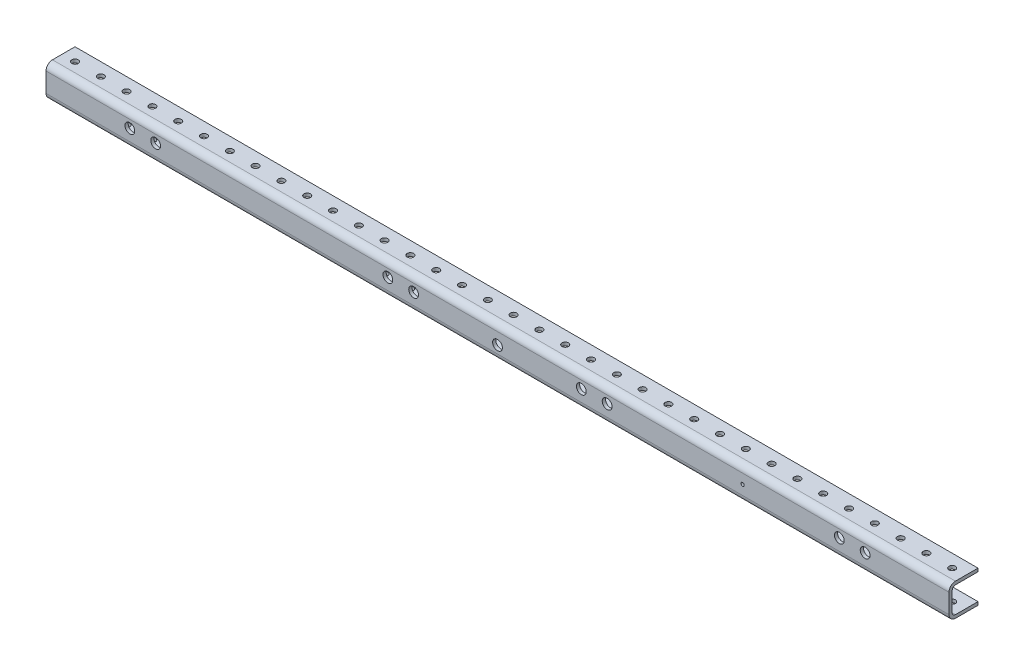
SolidWorks part; units mm, degrees
material "6061-T6 (SS)"
ref_plane "Front Plane" through (0, 0, 0) normal (0, 0, 1) x (1, 0, 0)
ref_plane "Top Plane" through (0, 0, 0) normal (0, 1, 0) x (1, 0, 0)
ref_plane "Right Plane" through (0, 0, 0) normal (1, 0, 0) x (0, 0, -1)
ref_plane "Plane1" through (0, 0, 3.175) normal (0, 0, 1) x (1, 0, 0)
sketch "Sketch1" plane through (0, 0, 3.175) normal (0, 0, 1) x (1, 0, 0)
  line L0 (872.98, -7.202) -> (872.98, 24.548)
  line L1 (872.98, 24.548) -> (-16.02, 24.548)
  line L2 (-16.02, 24.548) -> (-16.02, -7.202)
  line L3 (-16.02, -7.202) -> (872.98, -7.202)
extrude "Extrude1" add sketch "Sketch1" against normal blind 28.575
sketch "Sketch2" plane through (-16.02, 0, 0) normal (-1, 0, 0) x (0, 0, 1)
  line L0 (-25.4, 21.373) -> (-25.4, -4.027)
  line L1 (-25.4, -4.027) -> (0, -4.027)
  line L2 (0, -4.027) -> (0, 21.373)
  line L3 (0, 21.373) -> (-25.4, 21.373)
extrude "Extrude2" cut sketch "Sketch2" against normal through all
hole_wizard "Hole1" positions "Sketch4" profile "Sketch3" legacy
sketch "Sketch4" plane through (0, -4.027, 0) normal (0, 1, 0) x (-1, 0, 0)
  point P0 (3.32, -12.7)
sketch "Sketch3" plane through (-3.32, -4.027, -12.7) normal (1, 0, 0) x (0, 0, 1)
  line L0 (0, 0) -> (0, 3.175)
  line L1 (0, 3.175) -> (3.175, 3.175)
  line L2 (3.175, 3.175) -> (3.175, 0)
  line L3 (3.175, 0) -> (0, 0)
  line L4 (0, 110) -> (0, -10) construction
  dimension "Diameter" = 6.35
  dimension "Depth" = 3.175
hole_wizard "Hole2" positions "Sketch6" profile "Sketch5" legacy
sketch "Sketch6" plane through (0, -4.027, 0) normal (0, 1, 0) x (-1, 0, 0)
  point P0 (-22.08, -12.7)
sketch "Sketch5" plane through (22.08, -4.027, -12.7) normal (1, 0, 0) x (0, 0, 1)
  line L0 (0, 0) -> (0, 3.175)
  line L1 (0, 3.175) -> (3.175, 3.175)
  line L2 (3.175, 3.175) -> (3.175, 0)
  line L3 (3.175, 0) -> (0, 0)
  line L4 (0, 110) -> (0, -10) construction
  dimension "Diameter" = 6.35
  dimension "Depth" = 3.175
hole_wizard "Hole3" positions "Sketch8" profile "Sketch7" legacy
sketch "Sketch8" plane through (0, -4.027, 0) normal (0, 1, 0) x (-1, 0, 0)
  point P0 (-47.48, -12.7)
sketch "Sketch7" plane through (47.48, -4.027, -12.7) normal (1, 0, 0) x (0, 0, 1)
  line L0 (0, 0) -> (0, 3.175)
  line L1 (0, 3.175) -> (3.175, 3.175)
  line L2 (3.175, 3.175) -> (3.175, 0)
  line L3 (3.175, 0) -> (0, 0)
  line L4 (0, 110) -> (0, -10) construction
  dimension "Diameter" = 6.35
  dimension "Depth" = 3.175
hole_wizard "Hole4" positions "Sketch10" profile "Sketch9" legacy
sketch "Sketch10" plane through (0, -4.027, 0) normal (0, 1, 0) x (-1, 0, 0)
  point P0 (-72.88, -12.7)
sketch "Sketch9" plane through (72.88, -4.027, -12.7) normal (1, 0, 0) x (0, 0, 1)
  line L0 (0, 0) -> (0, 3.175)
  line L1 (0, 3.175) -> (3.175, 3.175)
  line L2 (3.175, 3.175) -> (3.175, 0)
  line L3 (3.175, 0) -> (0, 0)
  line L4 (0, 110) -> (0, -10) construction
  dimension "Diameter" = 6.35
  dimension "Depth" = 3.175
hole_wizard "Hole5" positions "Sketch12" profile "Sketch11" legacy
sketch "Sketch12" plane through (0, -4.027, 0) normal (0, 1, 0) x (-1, 0, 0)
  point P0 (-98.28, -12.7)
sketch "Sketch11" plane through (98.28, -4.027, -12.7) normal (1, 0, 0) x (0, 0, 1)
  line L0 (0, 0) -> (0, 3.175)
  line L1 (0, 3.175) -> (3.175, 3.175)
  line L2 (3.175, 3.175) -> (3.175, 0)
  line L3 (3.175, 0) -> (0, 0)
  line L4 (0, 110) -> (0, -10) construction
  dimension "Diameter" = 6.35
  dimension "Depth" = 3.175
hole_wizard "Hole6" positions "Sketch14" profile "Sketch13" legacy
sketch "Sketch14" plane through (0, -4.027, 0) normal (0, 1, 0) x (-1, 0, 0)
  point P0 (-123.68, -12.7)
sketch "Sketch13" plane through (123.68, -4.027, -12.7) normal (1, 0, 0) x (0, 0, 1)
  line L0 (0, 0) -> (0, 3.175)
  line L1 (0, 3.175) -> (3.175, 3.175)
  line L2 (3.175, 3.175) -> (3.175, 0)
  line L3 (3.175, 0) -> (0, 0)
  line L4 (0, 110) -> (0, -10) construction
  dimension "Diameter" = 6.35
  dimension "Depth" = 3.175
hole_wizard "Hole7" positions "Sketch16" profile "Sketch15" legacy
sketch "Sketch16" plane through (0, -4.027, 0) normal (0, 1, 0) x (-1, 0, 0)
  point P0 (-149.08, -12.7)
sketch "Sketch15" plane through (149.08, -4.027, -12.7) normal (1, 0, 0) x (0, 0, 1)
  line L0 (0, 0) -> (0, 3.175)
  line L1 (0, 3.175) -> (3.175, 3.175)
  line L2 (3.175, 3.175) -> (3.175, 0)
  line L3 (3.175, 0) -> (0, 0)
  line L4 (0, 110) -> (0, -10) construction
  dimension "Diameter" = 6.35
  dimension "Depth" = 3.175
hole_wizard "Hole8" positions "Sketch18" profile "Sketch17" legacy
sketch "Sketch18" plane through (0, -4.027, 0) normal (0, 1, 0) x (-1, 0, 0)
  point P0 (-174.48, -12.7)
sketch "Sketch17" plane through (174.48, -4.027, -12.7) normal (1, 0, 0) x (0, 0, 1)
  line L0 (0, 0) -> (0, 3.175)
  line L1 (0, 3.175) -> (3.175, 3.175)
  line L2 (3.175, 3.175) -> (3.175, 0)
  line L3 (3.175, 0) -> (0, 0)
  line L4 (0, 110) -> (0, -10) construction
  dimension "Diameter" = 6.35
  dimension "Depth" = 3.175
hole_wizard "Hole9" positions "Sketch20" profile "Sketch19" legacy
sketch "Sketch20" plane through (0, -4.027, 0) normal (0, 1, 0) x (-1, 0, 0)
  point P0 (-199.88, -12.7)
sketch "Sketch19" plane through (199.88, -4.027, -12.7) normal (1, 0, 0) x (0, 0, 1)
  line L0 (0, 0) -> (0, 3.175)
  line L1 (0, 3.175) -> (3.175, 3.175)
  line L2 (3.175, 3.175) -> (3.175, 0)
  line L3 (3.175, 0) -> (0, 0)
  line L4 (0, 110) -> (0, -10) construction
  dimension "Diameter" = 6.35
  dimension "Depth" = 3.175
hole_wizard "Hole10" positions "Sketch22" profile "Sketch21" legacy
sketch "Sketch22" plane through (0, -4.027, 0) normal (0, 1, 0) x (-1, 0, 0)
  point P0 (-225.28, -12.7)
sketch "Sketch21" plane through (225.28, -4.027, -12.7) normal (1, 0, 0) x (0, 0, 1)
  line L0 (0, 0) -> (0, 3.175)
  line L1 (0, 3.175) -> (3.175, 3.175)
  line L2 (3.175, 3.175) -> (3.175, 0)
  line L3 (3.175, 0) -> (0, 0)
  line L4 (0, 110) -> (0, -10) construction
  dimension "Diameter" = 6.35
  dimension "Depth" = 3.175
hole_wizard "Hole11" positions "Sketch24" profile "Sketch23" legacy
sketch "Sketch24" plane through (0, -4.027, 0) normal (0, 1, 0) x (-1, 0, 0)
  point P0 (-250.68, -12.7)
sketch "Sketch23" plane through (250.68, -4.027, -12.7) normal (1, 0, 0) x (0, 0, 1)
  line L0 (0, 0) -> (0, 3.175)
  line L1 (0, 3.175) -> (3.175, 3.175)
  line L2 (3.175, 3.175) -> (3.175, 0)
  line L3 (3.175, 0) -> (0, 0)
  line L4 (0, 110) -> (0, -10) construction
  dimension "Diameter" = 6.35
  dimension "Depth" = 3.175
hole_wizard "Hole12" positions "Sketch26" profile "Sketch25" legacy
sketch "Sketch26" plane through (0, -4.027, 0) normal (0, 1, 0) x (-1, 0, 0)
  point P0 (-276.08, -12.7)
sketch "Sketch25" plane through (276.08, -4.027, -12.7) normal (1, 0, 0) x (0, 0, 1)
  line L0 (0, 0) -> (0, 3.175)
  line L1 (0, 3.175) -> (3.175, 3.175)
  line L2 (3.175, 3.175) -> (3.175, 0)
  line L3 (3.175, 0) -> (0, 0)
  line L4 (0, 110) -> (0, -10) construction
  dimension "Diameter" = 6.35
  dimension "Depth" = 3.175
hole_wizard "Hole13" positions "Sketch28" profile "Sketch27" legacy
sketch "Sketch28" plane through (0, -4.027, 0) normal (0, 1, 0) x (-1, 0, 0)
  point P0 (-301.48, -12.7)
sketch "Sketch27" plane through (301.48, -4.027, -12.7) normal (1, 0, 0) x (0, 0, 1)
  line L0 (0, 0) -> (0, 3.175)
  line L1 (0, 3.175) -> (3.175, 3.175)
  line L2 (3.175, 3.175) -> (3.175, 0)
  line L3 (3.175, 0) -> (0, 0)
  line L4 (0, 110) -> (0, -10) construction
  dimension "Diameter" = 6.35
  dimension "Depth" = 3.175
hole_wizard "Hole14" positions "Sketch30" profile "Sketch29" legacy
sketch "Sketch30" plane through (0, -4.027, 0) normal (0, 1, 0) x (-1, 0, 0)
  point P0 (-326.88, -12.7)
sketch "Sketch29" plane through (326.88, -4.027, -12.7) normal (1, 0, 0) x (0, 0, 1)
  line L0 (0, 0) -> (0, 3.175)
  line L1 (0, 3.175) -> (3.175, 3.175)
  line L2 (3.175, 3.175) -> (3.175, 0)
  line L3 (3.175, 0) -> (0, 0)
  line L4 (0, 110) -> (0, -10) construction
  dimension "Diameter" = 6.35
  dimension "Depth" = 3.175
hole_wizard "Hole15" positions "Sketch32" profile "Sketch31" legacy
sketch "Sketch32" plane through (0, -4.027, 0) normal (0, 1, 0) x (-1, 0, 0)
  point P0 (-352.28, -12.7)
sketch "Sketch31" plane through (352.28, -4.027, -12.7) normal (1, 0, 0) x (0, 0, 1)
  line L0 (0, 0) -> (0, 3.175)
  line L1 (0, 3.175) -> (3.175, 3.175)
  line L2 (3.175, 3.175) -> (3.175, 0)
  line L3 (3.175, 0) -> (0, 0)
  line L4 (0, 110) -> (0, -10) construction
  dimension "Diameter" = 6.35
  dimension "Depth" = 3.175
hole_wizard "Hole16" positions "Sketch34" profile "Sketch33" legacy
sketch "Sketch34" plane through (0, -4.027, 0) normal (0, 1, 0) x (-1, 0, 0)
  point P0 (-377.68, -12.7)
sketch "Sketch33" plane through (377.68, -4.027, -12.7) normal (1, 0, 0) x (0, 0, 1)
  line L0 (0, 0) -> (0, 3.175)
  line L1 (0, 3.175) -> (3.175, 3.175)
  line L2 (3.175, 3.175) -> (3.175, 0)
  line L3 (3.175, 0) -> (0, 0)
  line L4 (0, 110) -> (0, -10) construction
  dimension "Diameter" = 6.35
  dimension "Depth" = 3.175
hole_wizard "Hole17" positions "Sketch36" profile "Sketch35" legacy
sketch "Sketch36" plane through (0, -4.027, 0) normal (0, 1, 0) x (-1, 0, 0)
  point P0 (-403.08, -12.7)
sketch "Sketch35" plane through (403.08, -4.027, -12.7) normal (1, 0, 0) x (0, 0, 1)
  line L0 (0, 0) -> (0, 3.175)
  line L1 (0, 3.175) -> (3.175, 3.175)
  line L2 (3.175, 3.175) -> (3.175, 0)
  line L3 (3.175, 0) -> (0, 0)
  line L4 (0, 110) -> (0, -10) construction
  dimension "Diameter" = 6.35
  dimension "Depth" = 3.175
hole_wizard "Hole18" positions "Sketch38" profile "Sketch37" legacy
sketch "Sketch38" plane through (0, -4.027, 0) normal (0, 1, 0) x (-1, 0, 0)
  point P0 (-428.48, -12.7)
sketch "Sketch37" plane through (428.48, -4.027, -12.7) normal (1, 0, 0) x (0, 0, 1)
  line L0 (0, 0) -> (0, 3.175)
  line L1 (0, 3.175) -> (3.175, 3.175)
  line L2 (3.175, 3.175) -> (3.175, 0)
  line L3 (3.175, 0) -> (0, 0)
  line L4 (0, 110) -> (0, -10) construction
  dimension "Diameter" = 6.35
  dimension "Depth" = 3.175
hole_wizard "Hole19" positions "Sketch40" profile "Sketch39" legacy
sketch "Sketch40" plane through (0, -4.027, 0) normal (0, 1, 0) x (-1, 0, 0)
  point P0 (-453.88, -12.7)
sketch "Sketch39" plane through (453.88, -4.027, -12.7) normal (1, 0, 0) x (0, 0, 1)
  line L0 (0, 0) -> (0, 3.175)
  line L1 (0, 3.175) -> (3.175, 3.175)
  line L2 (3.175, 3.175) -> (3.175, 0)
  line L3 (3.175, 0) -> (0, 0)
  line L4 (0, 110) -> (0, -10) construction
  dimension "Diameter" = 6.35
  dimension "Depth" = 3.175
hole_wizard "Hole20" positions "Sketch42" profile "Sketch41" legacy
sketch "Sketch42" plane through (0, -4.027, 0) normal (0, 1, 0) x (-1, 0, 0)
  point P0 (-479.28, -12.7)
sketch "Sketch41" plane through (479.28, -4.027, -12.7) normal (1, 0, 0) x (0, 0, 1)
  line L0 (0, 0) -> (0, 3.175)
  line L1 (0, 3.175) -> (3.175, 3.175)
  line L2 (3.175, 3.175) -> (3.175, 0)
  line L3 (3.175, 0) -> (0, 0)
  line L4 (0, 110) -> (0, -10) construction
  dimension "Diameter" = 6.35
  dimension "Depth" = 3.175
hole_wizard "Hole21" positions "Sketch44" profile "Sketch43" legacy
sketch "Sketch44" plane through (0, -4.027, 0) normal (0, 1, 0) x (-1, 0, 0)
  point P0 (-504.68, -12.7)
sketch "Sketch43" plane through (504.68, -4.027, -12.7) normal (1, 0, 0) x (0, 0, 1)
  line L0 (0, 0) -> (0, 3.175)
  line L1 (0, 3.175) -> (3.175, 3.175)
  line L2 (3.175, 3.175) -> (3.175, 0)
  line L3 (3.175, 0) -> (0, 0)
  line L4 (0, 110) -> (0, -10) construction
  dimension "Diameter" = 6.35
  dimension "Depth" = 3.175
hole_wizard "Hole22" positions "Sketch46" profile "Sketch45" legacy
sketch "Sketch46" plane through (0, -4.027, 0) normal (0, 1, 0) x (-1, 0, 0)
  point P0 (-530.08, -12.7)
sketch "Sketch45" plane through (530.08, -4.027, -12.7) normal (1, 0, 0) x (0, 0, 1)
  line L0 (0, 0) -> (0, 3.175)
  line L1 (0, 3.175) -> (3.175, 3.175)
  line L2 (3.175, 3.175) -> (3.175, 0)
  line L3 (3.175, 0) -> (0, 0)
  line L4 (0, 110) -> (0, -10) construction
  dimension "Diameter" = 6.35
  dimension "Depth" = 3.175
hole_wizard "Hole23" positions "Sketch48" profile "Sketch47" legacy
sketch "Sketch48" plane through (0, -4.027, 0) normal (0, 1, 0) x (-1, 0, 0)
  point P0 (-555.48, -12.7)
sketch "Sketch47" plane through (555.48, -4.027, -12.7) normal (1, 0, 0) x (0, 0, 1)
  line L0 (0, 0) -> (0, 3.175)
  line L1 (0, 3.175) -> (3.175, 3.175)
  line L2 (3.175, 3.175) -> (3.175, 0)
  line L3 (3.175, 0) -> (0, 0)
  line L4 (0, 110) -> (0, -10) construction
  dimension "Diameter" = 6.35
  dimension "Depth" = 3.175
hole_wizard "Hole24" positions "Sketch50" profile "Sketch49" legacy
sketch "Sketch50" plane through (0, -4.027, 0) normal (0, 1, 0) x (-1, 0, 0)
  point P0 (-580.88, -12.7)
sketch "Sketch49" plane through (580.88, -4.027, -12.7) normal (1, 0, 0) x (0, 0, 1)
  line L0 (0, 0) -> (0, 3.175)
  line L1 (0, 3.175) -> (3.175, 3.175)
  line L2 (3.175, 3.175) -> (3.175, 0)
  line L3 (3.175, 0) -> (0, 0)
  line L4 (0, 110) -> (0, -10) construction
  dimension "Diameter" = 6.35
  dimension "Depth" = 3.175
hole_wizard "Hole25" positions "Sketch52" profile "Sketch51" legacy
sketch "Sketch52" plane through (0, -4.027, 0) normal (0, 1, 0) x (-1, 0, 0)
  point P0 (-606.28, -12.7)
sketch "Sketch51" plane through (606.28, -4.027, -12.7) normal (1, 0, 0) x (0, 0, 1)
  line L0 (0, 0) -> (0, 3.175)
  line L1 (0, 3.175) -> (3.175, 3.175)
  line L2 (3.175, 3.175) -> (3.175, 0)
  line L3 (3.175, 0) -> (0, 0)
  line L4 (0, 110) -> (0, -10) construction
  dimension "Diameter" = 6.35
  dimension "Depth" = 3.175
hole_wizard "Hole26" positions "Sketch54" profile "Sketch53" legacy
sketch "Sketch54" plane through (0, -4.027, 0) normal (0, 1, 0) x (-1, 0, 0)
  point P0 (-631.68, -12.7)
sketch "Sketch53" plane through (631.68, -4.027, -12.7) normal (1, 0, 0) x (0, 0, 1)
  line L0 (0, 0) -> (0, 3.175)
  line L1 (0, 3.175) -> (3.175, 3.175)
  line L2 (3.175, 3.175) -> (3.175, 0)
  line L3 (3.175, 0) -> (0, 0)
  line L4 (0, 110) -> (0, -10) construction
  dimension "Diameter" = 6.35
  dimension "Depth" = 3.175
hole_wizard "Hole27" positions "Sketch56" profile "Sketch55" legacy
sketch "Sketch56" plane through (0, -4.027, 0) normal (0, 1, 0) x (-1, 0, 0)
  point P0 (-657.08, -12.7)
sketch "Sketch55" plane through (657.08, -4.027, -12.7) normal (1, 0, 0) x (0, 0, 1)
  line L0 (0, 0) -> (0, 3.175)
  line L1 (0, 3.175) -> (3.175, 3.175)
  line L2 (3.175, 3.175) -> (3.175, 0)
  line L3 (3.175, 0) -> (0, 0)
  line L4 (0, 110) -> (0, -10) construction
  dimension "Diameter" = 6.35
  dimension "Depth" = 3.175
hole_wizard "Hole28" positions "Sketch58" profile "Sketch57" legacy
sketch "Sketch58" plane through (0, -4.027, 0) normal (0, 1, 0) x (-1, 0, 0)
  point P0 (-682.48, -12.7)
sketch "Sketch57" plane through (682.48, -4.027, -12.7) normal (1, 0, 0) x (0, 0, 1)
  line L0 (0, 0) -> (0, 3.175)
  line L1 (0, 3.175) -> (3.175, 3.175)
  line L2 (3.175, 3.175) -> (3.175, 0)
  line L3 (3.175, 0) -> (0, 0)
  line L4 (0, 110) -> (0, -10) construction
  dimension "Diameter" = 6.35
  dimension "Depth" = 3.175
hole_wizard "Hole29" positions "Sketch60" profile "Sketch59" legacy
sketch "Sketch60" plane through (0, -4.027, 0) normal (0, 1, 0) x (-1, 0, 0)
  point P0 (-707.88, -12.7)
sketch "Sketch59" plane through (707.88, -4.027, -12.7) normal (1, 0, 0) x (0, 0, 1)
  line L0 (0, 0) -> (0, 3.175)
  line L1 (0, 3.175) -> (3.175, 3.175)
  line L2 (3.175, 3.175) -> (3.175, 0)
  line L3 (3.175, 0) -> (0, 0)
  line L4 (0, 110) -> (0, -10) construction
  dimension "Diameter" = 6.35
  dimension "Depth" = 3.175
hole_wizard "Hole30" positions "Sketch62" profile "Sketch61" legacy
sketch "Sketch62" plane through (0, -4.027, 0) normal (0, 1, 0) x (-1, 0, 0)
  point P0 (-733.28, -12.7)
sketch "Sketch61" plane through (733.28, -4.027, -12.7) normal (1, 0, 0) x (0, 0, 1)
  line L0 (0, 0) -> (0, 3.175)
  line L1 (0, 3.175) -> (3.175, 3.175)
  line L2 (3.175, 3.175) -> (3.175, 0)
  line L3 (3.175, 0) -> (0, 0)
  line L4 (0, 110) -> (0, -10) construction
  dimension "Diameter" = 6.35
  dimension "Depth" = 3.175
hole_wizard "Hole31" positions "Sketch64" profile "Sketch63" legacy
sketch "Sketch64" plane through (0, -4.027, 0) normal (0, 1, 0) x (-1, 0, 0)
  point P0 (-758.68, -12.7)
sketch "Sketch63" plane through (758.68, -4.027, -12.7) normal (1, 0, 0) x (0, 0, 1)
  line L0 (0, 0) -> (0, 3.175)
  line L1 (0, 3.175) -> (3.175, 3.175)
  line L2 (3.175, 3.175) -> (3.175, 0)
  line L3 (3.175, 0) -> (0, 0)
  line L4 (0, 110) -> (0, -10) construction
  dimension "Diameter" = 6.35
  dimension "Depth" = 3.175
hole_wizard "Hole32" positions "Sketch66" profile "Sketch65" legacy
sketch "Sketch66" plane through (0, -4.027, 0) normal (0, 1, 0) x (-1, 0, 0)
  point P0 (-784.08, -12.7)
sketch "Sketch65" plane through (784.08, -4.027, -12.7) normal (1, 0, 0) x (0, 0, 1)
  line L0 (0, 0) -> (0, 3.175)
  line L1 (0, 3.175) -> (3.175, 3.175)
  line L2 (3.175, 3.175) -> (3.175, 0)
  line L3 (3.175, 0) -> (0, 0)
  line L4 (0, 110) -> (0, -10) construction
  dimension "Diameter" = 6.35
  dimension "Depth" = 3.175
hole_wizard "Hole33" positions "Sketch68" profile "Sketch67" legacy
sketch "Sketch68" plane through (0, -4.027, 0) normal (0, 1, 0) x (-1, 0, 0)
  point P0 (-809.48, -12.7)
sketch "Sketch67" plane through (809.48, -4.027, -12.7) normal (1, 0, 0) x (0, 0, 1)
  line L0 (0, 0) -> (0, 3.175)
  line L1 (0, 3.175) -> (3.175, 3.175)
  line L2 (3.175, 3.175) -> (3.175, 0)
  line L3 (3.175, 0) -> (0, 0)
  line L4 (0, 110) -> (0, -10) construction
  dimension "Diameter" = 6.35
  dimension "Depth" = 3.175
hole_wizard "Hole34" positions "Sketch70" profile "Sketch69" legacy
sketch "Sketch70" plane through (0, -4.027, 0) normal (0, 1, 0) x (-1, 0, 0)
  point P0 (-834.88, -12.7)
sketch "Sketch69" plane through (834.88, -4.027, -12.7) normal (1, 0, 0) x (0, 0, 1)
  line L0 (0, 0) -> (0, 3.175)
  line L1 (0, 3.175) -> (3.175, 3.175)
  line L2 (3.175, 3.175) -> (3.175, 0)
  line L3 (3.175, 0) -> (0, 0)
  line L4 (0, 110) -> (0, -10) construction
  dimension "Diameter" = 6.35
  dimension "Depth" = 3.175
hole_wizard "Hole35" positions "Sketch72" profile "Sketch71" legacy
sketch "Sketch72" plane through (0, -4.027, 0) normal (0, 1, 0) x (-1, 0, 0)
  point P0 (-860.28, -12.7)
sketch "Sketch71" plane through (860.28, -4.027, -12.7) normal (1, 0, 0) x (0, 0, 1)
  line L0 (0, 0) -> (0, 3.175)
  line L1 (0, 3.175) -> (3.175, 3.175)
  line L2 (3.175, 3.175) -> (3.175, 0)
  line L3 (3.175, 0) -> (0, 0)
  line L4 (0, 110) -> (0, -10) construction
  dimension "Diameter" = 6.35
  dimension "Depth" = 3.175
hole_wizard "Hole36" positions "Sketch74" profile "Sketch73" legacy
sketch "Sketch74" plane through (0, 0, 3.175) normal (0, 0, 1) x (1, 0, 0)
  point P0 (91.93, 10.578)
sketch "Sketch73" plane through (91.93, 10.578, 3.175) normal (1, 0, 0) x (0, -1, 0)
  line L0 (0, 0) -> (0, 28.575)
  line L1 (0, 28.575) -> (4.826, 28.575)
  line L2 (4.826, 28.575) -> (4.826, 0)
  line L3 (4.826, 0) -> (0, 0)
  line L4 (0, 110) -> (0, -10) construction
  dimension "Diameter" = 9.652
  dimension "Depth" = 28.575
hole_wizard "Hole37" positions "Sketch76" profile "Sketch75" legacy
sketch "Sketch76" plane through (0, 0, 3.175) normal (0, 0, 1) x (1, 0, 0)
  point P0 (66.53, 10.578)
sketch "Sketch75" plane through (66.53, 10.578, 3.175) normal (1, 0, 0) x (0, -1, 0)
  line L0 (0, 0) -> (0, 28.575)
  line L1 (0, 28.575) -> (4.826, 28.575)
  line L2 (4.826, 28.575) -> (4.826, 0)
  line L3 (4.826, 0) -> (0, 0)
  line L4 (0, 110) -> (0, -10) construction
  dimension "Diameter" = 9.652
  dimension "Depth" = 28.575
hole_wizard "Hole38" positions "Sketch78" profile "Sketch77" legacy
sketch "Sketch78" plane through (0, 0, 3.175) normal (0, 0, 1) x (1, 0, 0)
  point P0 (765.03, 10.578)
sketch "Sketch77" plane through (765.03, 10.578, 3.175) normal (1, 0, 0) x (0, -1, 0)
  line L0 (0, 0) -> (0, 28.575)
  line L1 (0, 28.575) -> (4.826, 28.575)
  line L2 (4.826, 28.575) -> (4.826, 0)
  line L3 (4.826, 0) -> (0, 0)
  line L4 (0, 110) -> (0, -10) construction
  dimension "Diameter" = 9.652
  dimension "Depth" = 28.575
hole_wizard "Hole39" positions "Sketch80" profile "Sketch79" legacy
sketch "Sketch80" plane through (0, 0, 3.175) normal (0, 0, 1) x (1, 0, 0)
  point P0 (790.43, 10.578)
sketch "Sketch79" plane through (790.43, 10.578, 3.175) normal (1, 0, 0) x (0, -1, 0)
  line L0 (0, 0) -> (0, 28.575)
  line L1 (0, 28.575) -> (4.826, 28.575)
  line L2 (4.826, 28.575) -> (4.826, 0)
  line L3 (4.826, 0) -> (0, 0)
  line L4 (0, 110) -> (0, -10) construction
  dimension "Diameter" = 9.652
  dimension "Depth" = 28.575
hole_wizard "Hole40" positions "Sketch82" profile "Sketch81" legacy
sketch "Sketch82" plane through (0, 0, 3.175) normal (0, 0, 1) x (1, 0, 0)
  point P0 (428.48, 6.768)
sketch "Sketch81" plane through (428.48, 6.768, 3.175) normal (1, 0, 0) x (0, -1, 0)
  line L0 (0, 0) -> (0, 28.575)
  line L1 (0, 28.575) -> (4.826, 28.575)
  line L2 (4.826, 28.575) -> (4.826, 0)
  line L3 (4.826, 0) -> (0, 0)
  line L4 (0, 110) -> (0, -10) construction
  dimension "Diameter" = 9.652
  dimension "Depth" = 28.575
hole_wizard "Hole41" positions "Sketch84" profile "Sketch83" legacy
sketch "Sketch84" plane through (0, 0, 3.175) normal (0, 0, 1) x (1, 0, 0)
  point P0 (536.43, 10.578)
sketch "Sketch83" plane through (536.43, 10.578, 3.175) normal (1, 0, 0) x (0, -1, 0)
  line L0 (0, 0) -> (0, 28.575)
  line L1 (0, 28.575) -> (4.826, 28.575)
  line L2 (4.826, 28.575) -> (4.826, 0)
  line L3 (4.826, 0) -> (0, 0)
  line L4 (0, 110) -> (0, -10) construction
  dimension "Diameter" = 9.652
  dimension "Depth" = 28.575
hole_wizard "Hole42" positions "Sketch86" profile "Sketch85" legacy
sketch "Sketch86" plane through (0, 0, 3.175) normal (0, 0, 1) x (1, 0, 0)
  point P0 (511.03, 10.578)
sketch "Sketch85" plane through (511.03, 10.578, 3.175) normal (1, 0, 0) x (0, -1, 0)
  line L0 (0, 0) -> (0, 28.575)
  line L1 (0, 28.575) -> (4.826, 28.575)
  line L2 (4.826, 28.575) -> (4.826, 0)
  line L3 (4.826, 0) -> (0, 0)
  line L4 (0, 110) -> (0, -10) construction
  dimension "Diameter" = 9.652
  dimension "Depth" = 28.575
hole_wizard "Hole43" positions "Sketch88" profile "Sketch87" legacy
sketch "Sketch88" plane through (0, 0, 3.175) normal (0, 0, 1) x (1, 0, 0)
  point P0 (345.93, 10.578)
sketch "Sketch87" plane through (345.93, 10.578, 3.175) normal (1, 0, 0) x (0, -1, 0)
  line L0 (0, 0) -> (0, 28.575)
  line L1 (0, 28.575) -> (4.826, 28.575)
  line L2 (4.826, 28.575) -> (4.826, 0)
  line L3 (4.826, 0) -> (0, 0)
  line L4 (0, 110) -> (0, -10) construction
  dimension "Diameter" = 9.652
  dimension "Depth" = 28.575
hole_wizard "Hole44" positions "Sketch90" profile "Sketch89" legacy
sketch "Sketch90" plane through (0, 0, 3.175) normal (0, 0, 1) x (1, 0, 0)
  point P0 (320.53, 10.578)
sketch "Sketch89" plane through (320.53, 10.578, 3.175) normal (1, 0, 0) x (0, -1, 0)
  line L0 (0, 0) -> (0, 28.575)
  line L1 (0, 28.575) -> (4.826, 28.575)
  line L2 (4.826, 28.575) -> (4.826, 0)
  line L3 (4.826, 0) -> (0, 0)
  line L4 (0, 110) -> (0, -10) construction
  dimension "Diameter" = 9.652
  dimension "Depth" = 28.575
hole_wizard "Hole45" positions "Sketch92" profile "Sketch91" legacy
sketch "Sketch92" plane through (0, 0, 3.175) normal (0, 0, 1) x (1, 0, 0)
  point P0 (669.78, 8.673)
sketch "Sketch91" plane through (669.78, 8.673, 3.175) normal (1, 0, 0) x (0, -1, 0)
  line L0 (0, 0) -> (0, 28.575)
  line L1 (0, 28.575) -> (1.5875, 28.575)
  line L2 (1.5875, 28.575) -> (1.5875, 0)
  line L3 (1.5875, 0) -> (0, 0)
  line L4 (0, 110) -> (0, -10) construction
  dimension "Diameter" = 3.175
  dimension "Depth" = 28.575
hole_wizard "Hole46" positions "Sketch94" profile "Sketch93" legacy
sketch "Sketch94" plane through (0, 24.548, 0) normal (0, 1, 0) x (-1, 0, 0)
  point P0 (3.32, -12.7)
sketch "Sketch93" plane through (-3.32, 24.548, -12.7) normal (1, 0, 0) x (0, 0, 1)
  line L0 (0, 0) -> (0, 31.75)
  line L1 (0, 31.75) -> (3.175, 31.75)
  line L2 (3.175, 31.75) -> (3.175, 0)
  line L3 (3.175, 0) -> (0, 0)
  line L4 (0, 110) -> (0, -10) construction
  dimension "Diameter" = 6.35
  dimension "Depth" = 31.75
hole_wizard "Hole47" positions "Sketch96" profile "Sketch95" legacy
sketch "Sketch96" plane through (0, 24.548, 0) normal (0, 1, 0) x (-1, 0, 0)
  point P0 (-22.08, -12.7)
sketch "Sketch95" plane through (22.08, 24.548, -12.7) normal (1, 0, 0) x (0, 0, 1)
  line L0 (0, 0) -> (0, 31.75)
  line L1 (0, 31.75) -> (3.175, 31.75)
  line L2 (3.175, 31.75) -> (3.175, 0)
  line L3 (3.175, 0) -> (0, 0)
  line L4 (0, 110) -> (0, -10) construction
  dimension "Diameter" = 6.35
  dimension "Depth" = 31.75
hole_wizard "Hole48" positions "Sketch98" profile "Sketch97" legacy
sketch "Sketch98" plane through (0, 24.548, 0) normal (0, 1, 0) x (-1, 0, 0)
  point P0 (-47.48, -12.7)
sketch "Sketch97" plane through (47.48, 24.548, -12.7) normal (1, 0, 0) x (0, 0, 1)
  line L0 (0, 0) -> (0, 31.75)
  line L1 (0, 31.75) -> (3.175, 31.75)
  line L2 (3.175, 31.75) -> (3.175, 0)
  line L3 (3.175, 0) -> (0, 0)
  line L4 (0, 110) -> (0, -10) construction
  dimension "Diameter" = 6.35
  dimension "Depth" = 31.75
hole_wizard "Hole49" positions "Sketch100" profile "Sketch99" legacy
sketch "Sketch100" plane through (0, 24.548, 0) normal (0, 1, 0) x (-1, 0, 0)
  point P0 (-72.88, -12.7)
sketch "Sketch99" plane through (72.88, 24.548, -12.7) normal (1, 0, 0) x (0, 0, 1)
  line L0 (0, 0) -> (0, 31.75)
  line L1 (0, 31.75) -> (3.175, 31.75)
  line L2 (3.175, 31.75) -> (3.175, 0)
  line L3 (3.175, 0) -> (0, 0)
  line L4 (0, 110) -> (0, -10) construction
  dimension "Diameter" = 6.35
  dimension "Depth" = 31.75
hole_wizard "Hole50" positions "Sketch102" profile "Sketch101" legacy
sketch "Sketch102" plane through (0, 24.548, 0) normal (0, 1, 0) x (-1, 0, 0)
  point P0 (-98.28, -12.7)
sketch "Sketch101" plane through (98.28, 24.548, -12.7) normal (1, 0, 0) x (0, 0, 1)
  line L0 (0, 0) -> (0, 31.75)
  line L1 (0, 31.75) -> (3.175, 31.75)
  line L2 (3.175, 31.75) -> (3.175, 0)
  line L3 (3.175, 0) -> (0, 0)
  line L4 (0, 110) -> (0, -10) construction
  dimension "Diameter" = 6.35
  dimension "Depth" = 31.75
hole_wizard "Hole51" positions "Sketch104" profile "Sketch103" legacy
sketch "Sketch104" plane through (0, 24.548, 0) normal (0, 1, 0) x (-1, 0, 0)
  point P0 (-123.68, -12.7)
sketch "Sketch103" plane through (123.68, 24.548, -12.7) normal (1, 0, 0) x (0, 0, 1)
  line L0 (0, 0) -> (0, 31.75)
  line L1 (0, 31.75) -> (3.175, 31.75)
  line L2 (3.175, 31.75) -> (3.175, 0)
  line L3 (3.175, 0) -> (0, 0)
  line L4 (0, 110) -> (0, -10) construction
  dimension "Diameter" = 6.35
  dimension "Depth" = 31.75
hole_wizard "Hole52" positions "Sketch106" profile "Sketch105" legacy
sketch "Sketch106" plane through (0, 24.548, 0) normal (0, 1, 0) x (-1, 0, 0)
  point P0 (-149.08, -12.7)
sketch "Sketch105" plane through (149.08, 24.548, -12.7) normal (1, 0, 0) x (0, 0, 1)
  line L0 (0, 0) -> (0, 31.75)
  line L1 (0, 31.75) -> (3.175, 31.75)
  line L2 (3.175, 31.75) -> (3.175, 0)
  line L3 (3.175, 0) -> (0, 0)
  line L4 (0, 110) -> (0, -10) construction
  dimension "Diameter" = 6.35
  dimension "Depth" = 31.75
hole_wizard "Hole53" positions "Sketch108" profile "Sketch107" legacy
sketch "Sketch108" plane through (0, 24.548, 0) normal (0, 1, 0) x (-1, 0, 0)
  point P0 (-174.48, -12.7)
sketch "Sketch107" plane through (174.48, 24.548, -12.7) normal (1, 0, 0) x (0, 0, 1)
  line L0 (0, 0) -> (0, 31.75)
  line L1 (0, 31.75) -> (3.175, 31.75)
  line L2 (3.175, 31.75) -> (3.175, 0)
  line L3 (3.175, 0) -> (0, 0)
  line L4 (0, 110) -> (0, -10) construction
  dimension "Diameter" = 6.35
  dimension "Depth" = 31.75
hole_wizard "Hole54" positions "Sketch110" profile "Sketch109" legacy
sketch "Sketch110" plane through (0, 24.548, 0) normal (0, 1, 0) x (-1, 0, 0)
  point P0 (-199.88, -12.7)
sketch "Sketch109" plane through (199.88, 24.548, -12.7) normal (1, 0, 0) x (0, 0, 1)
  line L0 (0, 0) -> (0, 31.75)
  line L1 (0, 31.75) -> (3.175, 31.75)
  line L2 (3.175, 31.75) -> (3.175, 0)
  line L3 (3.175, 0) -> (0, 0)
  line L4 (0, 110) -> (0, -10) construction
  dimension "Diameter" = 6.35
  dimension "Depth" = 31.75
hole_wizard "Hole55" positions "Sketch112" profile "Sketch111" legacy
sketch "Sketch112" plane through (0, 24.548, 0) normal (0, 1, 0) x (-1, 0, 0)
  point P0 (-225.28, -12.7)
sketch "Sketch111" plane through (225.28, 24.548, -12.7) normal (1, 0, 0) x (0, 0, 1)
  line L0 (0, 0) -> (0, 31.75)
  line L1 (0, 31.75) -> (3.175, 31.75)
  line L2 (3.175, 31.75) -> (3.175, 0)
  line L3 (3.175, 0) -> (0, 0)
  line L4 (0, 110) -> (0, -10) construction
  dimension "Diameter" = 6.35
  dimension "Depth" = 31.75
hole_wizard "Hole56" positions "Sketch114" profile "Sketch113" legacy
sketch "Sketch114" plane through (0, 24.548, 0) normal (0, 1, 0) x (-1, 0, 0)
  point P0 (-250.68, -12.7)
sketch "Sketch113" plane through (250.68, 24.548, -12.7) normal (1, 0, 0) x (0, 0, 1)
  line L0 (0, 0) -> (0, 31.75)
  line L1 (0, 31.75) -> (3.175, 31.75)
  line L2 (3.175, 31.75) -> (3.175, 0)
  line L3 (3.175, 0) -> (0, 0)
  line L4 (0, 110) -> (0, -10) construction
  dimension "Diameter" = 6.35
  dimension "Depth" = 31.75
hole_wizard "Hole57" positions "Sketch116" profile "Sketch115" legacy
sketch "Sketch116" plane through (0, 24.548, 0) normal (0, 1, 0) x (-1, 0, 0)
  point P0 (-276.08, -12.7)
sketch "Sketch115" plane through (276.08, 24.548, -12.7) normal (1, 0, 0) x (0, 0, 1)
  line L0 (0, 0) -> (0, 31.75)
  line L1 (0, 31.75) -> (3.175, 31.75)
  line L2 (3.175, 31.75) -> (3.175, 0)
  line L3 (3.175, 0) -> (0, 0)
  line L4 (0, 110) -> (0, -10) construction
  dimension "Diameter" = 6.35
  dimension "Depth" = 31.75
hole_wizard "Hole58" positions "Sketch118" profile "Sketch117" legacy
sketch "Sketch118" plane through (0, 24.548, 0) normal (0, 1, 0) x (-1, 0, 0)
  point P0 (-301.48, -12.7)
sketch "Sketch117" plane through (301.48, 24.548, -12.7) normal (1, 0, 0) x (0, 0, 1)
  line L0 (0, 0) -> (0, 31.75)
  line L1 (0, 31.75) -> (3.175, 31.75)
  line L2 (3.175, 31.75) -> (3.175, 0)
  line L3 (3.175, 0) -> (0, 0)
  line L4 (0, 110) -> (0, -10) construction
  dimension "Diameter" = 6.35
  dimension "Depth" = 31.75
hole_wizard "Hole59" positions "Sketch120" profile "Sketch119" legacy
sketch "Sketch120" plane through (0, 24.548, 0) normal (0, 1, 0) x (-1, 0, 0)
  point P0 (-326.88, -12.7)
sketch "Sketch119" plane through (326.88, 24.548, -12.7) normal (1, 0, 0) x (0, 0, 1)
  line L0 (0, 0) -> (0, 31.75)
  line L1 (0, 31.75) -> (3.175, 31.75)
  line L2 (3.175, 31.75) -> (3.175, 0)
  line L3 (3.175, 0) -> (0, 0)
  line L4 (0, 110) -> (0, -10) construction
  dimension "Diameter" = 6.35
  dimension "Depth" = 31.75
hole_wizard "Hole60" positions "Sketch122" profile "Sketch121" legacy
sketch "Sketch122" plane through (0, 24.548, 0) normal (0, 1, 0) x (-1, 0, 0)
  point P0 (-352.28, -12.7)
sketch "Sketch121" plane through (352.28, 24.548, -12.7) normal (1, 0, 0) x (0, 0, 1)
  line L0 (0, 0) -> (0, 31.75)
  line L1 (0, 31.75) -> (3.175, 31.75)
  line L2 (3.175, 31.75) -> (3.175, 0)
  line L3 (3.175, 0) -> (0, 0)
  line L4 (0, 110) -> (0, -10) construction
  dimension "Diameter" = 6.35
  dimension "Depth" = 31.75
hole_wizard "Hole61" positions "Sketch124" profile "Sketch123" legacy
sketch "Sketch124" plane through (0, 24.548, 0) normal (0, 1, 0) x (-1, 0, 0)
  point P0 (-377.68, -12.7)
sketch "Sketch123" plane through (377.68, 24.548, -12.7) normal (1, 0, 0) x (0, 0, 1)
  line L0 (0, 0) -> (0, 31.75)
  line L1 (0, 31.75) -> (3.175, 31.75)
  line L2 (3.175, 31.75) -> (3.175, 0)
  line L3 (3.175, 0) -> (0, 0)
  line L4 (0, 110) -> (0, -10) construction
  dimension "Diameter" = 6.35
  dimension "Depth" = 31.75
hole_wizard "Hole62" positions "Sketch126" profile "Sketch125" legacy
sketch "Sketch126" plane through (0, 24.548, 0) normal (0, 1, 0) x (-1, 0, 0)
  point P0 (-403.08, -12.7)
sketch "Sketch125" plane through (403.08, 24.548, -12.7) normal (1, 0, 0) x (0, 0, 1)
  line L0 (0, 0) -> (0, 31.75)
  line L1 (0, 31.75) -> (3.175, 31.75)
  line L2 (3.175, 31.75) -> (3.175, 0)
  line L3 (3.175, 0) -> (0, 0)
  line L4 (0, 110) -> (0, -10) construction
  dimension "Diameter" = 6.35
  dimension "Depth" = 31.75
hole_wizard "Hole63" positions "Sketch128" profile "Sketch127" legacy
sketch "Sketch128" plane through (0, 24.548, 0) normal (0, 1, 0) x (-1, 0, 0)
  point P0 (-428.48, -12.7)
sketch "Sketch127" plane through (428.48, 24.548, -12.7) normal (1, 0, 0) x (0, 0, 1)
  line L0 (0, 0) -> (0, 31.75)
  line L1 (0, 31.75) -> (3.175, 31.75)
  line L2 (3.175, 31.75) -> (3.175, 0)
  line L3 (3.175, 0) -> (0, 0)
  line L4 (0, 110) -> (0, -10) construction
  dimension "Diameter" = 6.35
  dimension "Depth" = 31.75
hole_wizard "Hole64" positions "Sketch130" profile "Sketch129" legacy
sketch "Sketch130" plane through (0, 24.548, 0) normal (0, 1, 0) x (-1, 0, 0)
  point P0 (-453.88, -12.7)
sketch "Sketch129" plane through (453.88, 24.548, -12.7) normal (1, 0, 0) x (0, 0, 1)
  line L0 (0, 0) -> (0, 31.75)
  line L1 (0, 31.75) -> (3.175, 31.75)
  line L2 (3.175, 31.75) -> (3.175, 0)
  line L3 (3.175, 0) -> (0, 0)
  line L4 (0, 110) -> (0, -10) construction
  dimension "Diameter" = 6.35
  dimension "Depth" = 31.75
hole_wizard "Hole65" positions "Sketch132" profile "Sketch131" legacy
sketch "Sketch132" plane through (0, 24.548, 0) normal (0, 1, 0) x (-1, 0, 0)
  point P0 (-479.28, -12.7)
sketch "Sketch131" plane through (479.28, 24.548, -12.7) normal (1, 0, 0) x (0, 0, 1)
  line L0 (0, 0) -> (0, 31.75)
  line L1 (0, 31.75) -> (3.175, 31.75)
  line L2 (3.175, 31.75) -> (3.175, 0)
  line L3 (3.175, 0) -> (0, 0)
  line L4 (0, 110) -> (0, -10) construction
  dimension "Diameter" = 6.35
  dimension "Depth" = 31.75
hole_wizard "Hole66" positions "Sketch134" profile "Sketch133" legacy
sketch "Sketch134" plane through (0, 24.548, 0) normal (0, 1, 0) x (-1, 0, 0)
  point P0 (-504.68, -12.7)
sketch "Sketch133" plane through (504.68, 24.548, -12.7) normal (1, 0, 0) x (0, 0, 1)
  line L0 (0, 0) -> (0, 31.75)
  line L1 (0, 31.75) -> (3.175, 31.75)
  line L2 (3.175, 31.75) -> (3.175, 0)
  line L3 (3.175, 0) -> (0, 0)
  line L4 (0, 110) -> (0, -10) construction
  dimension "Diameter" = 6.35
  dimension "Depth" = 31.75
hole_wizard "Hole67" positions "Sketch136" profile "Sketch135" legacy
sketch "Sketch136" plane through (0, 24.548, 0) normal (0, 1, 0) x (-1, 0, 0)
  point P0 (-530.08, -12.7)
sketch "Sketch135" plane through (530.08, 24.548, -12.7) normal (1, 0, 0) x (0, 0, 1)
  line L0 (0, 0) -> (0, 31.75)
  line L1 (0, 31.75) -> (3.175, 31.75)
  line L2 (3.175, 31.75) -> (3.175, 0)
  line L3 (3.175, 0) -> (0, 0)
  line L4 (0, 110) -> (0, -10) construction
  dimension "Diameter" = 6.35
  dimension "Depth" = 31.75
hole_wizard "Hole68" positions "Sketch138" profile "Sketch137" legacy
sketch "Sketch138" plane through (0, 24.548, 0) normal (0, 1, 0) x (-1, 0, 0)
  point P0 (-555.48, -12.7)
sketch "Sketch137" plane through (555.48, 24.548, -12.7) normal (1, 0, 0) x (0, 0, 1)
  line L0 (0, 0) -> (0, 31.75)
  line L1 (0, 31.75) -> (3.175, 31.75)
  line L2 (3.175, 31.75) -> (3.175, 0)
  line L3 (3.175, 0) -> (0, 0)
  line L4 (0, 110) -> (0, -10) construction
  dimension "Diameter" = 6.35
  dimension "Depth" = 31.75
hole_wizard "Hole69" positions "Sketch140" profile "Sketch139" legacy
sketch "Sketch140" plane through (0, 24.548, 0) normal (0, 1, 0) x (-1, 0, 0)
  point P0 (-580.88, -12.7)
sketch "Sketch139" plane through (580.88, 24.548, -12.7) normal (1, 0, 0) x (0, 0, 1)
  line L0 (0, 0) -> (0, 31.75)
  line L1 (0, 31.75) -> (3.175, 31.75)
  line L2 (3.175, 31.75) -> (3.175, 0)
  line L3 (3.175, 0) -> (0, 0)
  line L4 (0, 110) -> (0, -10) construction
  dimension "Diameter" = 6.35
  dimension "Depth" = 31.75
hole_wizard "Hole70" positions "Sketch142" profile "Sketch141" legacy
sketch "Sketch142" plane through (0, 24.548, 0) normal (0, 1, 0) x (-1, 0, 0)
  point P0 (-606.28, -12.7)
sketch "Sketch141" plane through (606.28, 24.548, -12.7) normal (1, 0, 0) x (0, 0, 1)
  line L0 (0, 0) -> (0, 31.75)
  line L1 (0, 31.75) -> (3.175, 31.75)
  line L2 (3.175, 31.75) -> (3.175, 0)
  line L3 (3.175, 0) -> (0, 0)
  line L4 (0, 110) -> (0, -10) construction
  dimension "Diameter" = 6.35
  dimension "Depth" = 31.75
hole_wizard "Hole71" positions "Sketch144" profile "Sketch143" legacy
sketch "Sketch144" plane through (0, 24.548, 0) normal (0, 1, 0) x (-1, 0, 0)
  point P0 (-631.68, -12.7)
sketch "Sketch143" plane through (631.68, 24.548, -12.7) normal (1, 0, 0) x (0, 0, 1)
  line L0 (0, 0) -> (0, 31.75)
  line L1 (0, 31.75) -> (3.175, 31.75)
  line L2 (3.175, 31.75) -> (3.175, 0)
  line L3 (3.175, 0) -> (0, 0)
  line L4 (0, 110) -> (0, -10) construction
  dimension "Diameter" = 6.35
  dimension "Depth" = 31.75
hole_wizard "Hole72" positions "Sketch146" profile "Sketch145" legacy
sketch "Sketch146" plane through (0, 24.548, 0) normal (0, 1, 0) x (-1, 0, 0)
  point P0 (-657.08, -12.7)
sketch "Sketch145" plane through (657.08, 24.548, -12.7) normal (1, 0, 0) x (0, 0, 1)
  line L0 (0, 0) -> (0, 31.75)
  line L1 (0, 31.75) -> (3.175, 31.75)
  line L2 (3.175, 31.75) -> (3.175, 0)
  line L3 (3.175, 0) -> (0, 0)
  line L4 (0, 110) -> (0, -10) construction
  dimension "Diameter" = 6.35
  dimension "Depth" = 31.75
hole_wizard "Hole73" positions "Sketch148" profile "Sketch147" legacy
sketch "Sketch148" plane through (0, 24.548, 0) normal (0, 1, 0) x (-1, 0, 0)
  point P0 (-682.48, -12.7)
sketch "Sketch147" plane through (682.48, 24.548, -12.7) normal (1, 0, 0) x (0, 0, 1)
  line L0 (0, 0) -> (0, 31.75)
  line L1 (0, 31.75) -> (3.175, 31.75)
  line L2 (3.175, 31.75) -> (3.175, 0)
  line L3 (3.175, 0) -> (0, 0)
  line L4 (0, 110) -> (0, -10) construction
  dimension "Diameter" = 6.35
  dimension "Depth" = 31.75
hole_wizard "Hole74" positions "Sketch150" profile "Sketch149" legacy
sketch "Sketch150" plane through (0, 24.548, 0) normal (0, 1, 0) x (-1, 0, 0)
  point P0 (-707.88, -12.7)
sketch "Sketch149" plane through (707.88, 24.548, -12.7) normal (1, 0, 0) x (0, 0, 1)
  line L0 (0, 0) -> (0, 31.75)
  line L1 (0, 31.75) -> (3.175, 31.75)
  line L2 (3.175, 31.75) -> (3.175, 0)
  line L3 (3.175, 0) -> (0, 0)
  line L4 (0, 110) -> (0, -10) construction
  dimension "Diameter" = 6.35
  dimension "Depth" = 31.75
hole_wizard "Hole75" positions "Sketch152" profile "Sketch151" legacy
sketch "Sketch152" plane through (0, 24.548, 0) normal (0, 1, 0) x (-1, 0, 0)
  point P0 (-733.28, -12.7)
sketch "Sketch151" plane through (733.28, 24.548, -12.7) normal (1, 0, 0) x (0, 0, 1)
  line L0 (0, 0) -> (0, 31.75)
  line L1 (0, 31.75) -> (3.175, 31.75)
  line L2 (3.175, 31.75) -> (3.175, 0)
  line L3 (3.175, 0) -> (0, 0)
  line L4 (0, 110) -> (0, -10) construction
  dimension "Diameter" = 6.35
  dimension "Depth" = 31.75
hole_wizard "Hole76" positions "Sketch154" profile "Sketch153" legacy
sketch "Sketch154" plane through (0, 24.548, 0) normal (0, 1, 0) x (-1, 0, 0)
  point P0 (-758.68, -12.7)
sketch "Sketch153" plane through (758.68, 24.548, -12.7) normal (1, 0, 0) x (0, 0, 1)
  line L0 (0, 0) -> (0, 31.75)
  line L1 (0, 31.75) -> (3.175, 31.75)
  line L2 (3.175, 31.75) -> (3.175, 0)
  line L3 (3.175, 0) -> (0, 0)
  line L4 (0, 110) -> (0, -10) construction
  dimension "Diameter" = 6.35
  dimension "Depth" = 31.75
hole_wizard "Hole77" positions "Sketch156" profile "Sketch155" legacy
sketch "Sketch156" plane through (0, 24.548, 0) normal (0, 1, 0) x (-1, 0, 0)
  point P0 (-784.08, -12.7)
sketch "Sketch155" plane through (784.08, 24.548, -12.7) normal (1, 0, 0) x (0, 0, 1)
  line L0 (0, 0) -> (0, 31.75)
  line L1 (0, 31.75) -> (3.175, 31.75)
  line L2 (3.175, 31.75) -> (3.175, 0)
  line L3 (3.175, 0) -> (0, 0)
  line L4 (0, 110) -> (0, -10) construction
  dimension "Diameter" = 6.35
  dimension "Depth" = 31.75
hole_wizard "Hole78" positions "Sketch158" profile "Sketch157" legacy
sketch "Sketch158" plane through (0, 24.548, 0) normal (0, 1, 0) x (-1, 0, 0)
  point P0 (-809.48, -12.7)
sketch "Sketch157" plane through (809.48, 24.548, -12.7) normal (1, 0, 0) x (0, 0, 1)
  line L0 (0, 0) -> (0, 31.75)
  line L1 (0, 31.75) -> (3.175, 31.75)
  line L2 (3.175, 31.75) -> (3.175, 0)
  line L3 (3.175, 0) -> (0, 0)
  line L4 (0, 110) -> (0, -10) construction
  dimension "Diameter" = 6.35
  dimension "Depth" = 31.75
hole_wizard "Hole79" positions "Sketch160" profile "Sketch159" legacy
sketch "Sketch160" plane through (0, 24.548, 0) normal (0, 1, 0) x (-1, 0, 0)
  point P0 (-834.88, -12.7)
sketch "Sketch159" plane through (834.88, 24.548, -12.7) normal (1, 0, 0) x (0, 0, 1)
  line L0 (0, 0) -> (0, 31.75)
  line L1 (0, 31.75) -> (3.175, 31.75)
  line L2 (3.175, 31.75) -> (3.175, 0)
  line L3 (3.175, 0) -> (0, 0)
  line L4 (0, 110) -> (0, -10) construction
  dimension "Diameter" = 6.35
  dimension "Depth" = 31.75
hole_wizard "Hole80" positions "Sketch162" profile "Sketch161" legacy
sketch "Sketch162" plane through (0, 24.548, 0) normal (0, 1, 0) x (-1, 0, 0)
  point P0 (-860.28, -12.7)
sketch "Sketch161" plane through (860.28, 24.548, -12.7) normal (1, 0, 0) x (0, 0, 1)
  line L0 (0, 0) -> (0, 31.75)
  line L1 (0, 31.75) -> (3.175, 31.75)
  line L2 (3.175, 31.75) -> (3.175, 0)
  line L3 (3.175, 0) -> (0, 0)
  line L4 (0, 110) -> (0, -10) construction
  dimension "Diameter" = 6.35
  dimension "Depth" = 31.75
fillet "Fillet1" radius 3.175 1 edges at (428.48, 21.373, 0)
fillet "Fillet2" radius 3.175 1 edges at (428.48, -4.027, 0)
fillet "Fillet3" radius 6.35 1 edges at (428.48, 24.548, 3.175)
fillet "Fillet4" radius 6.35 1 edges at (428.48, -7.202, 3.175)
